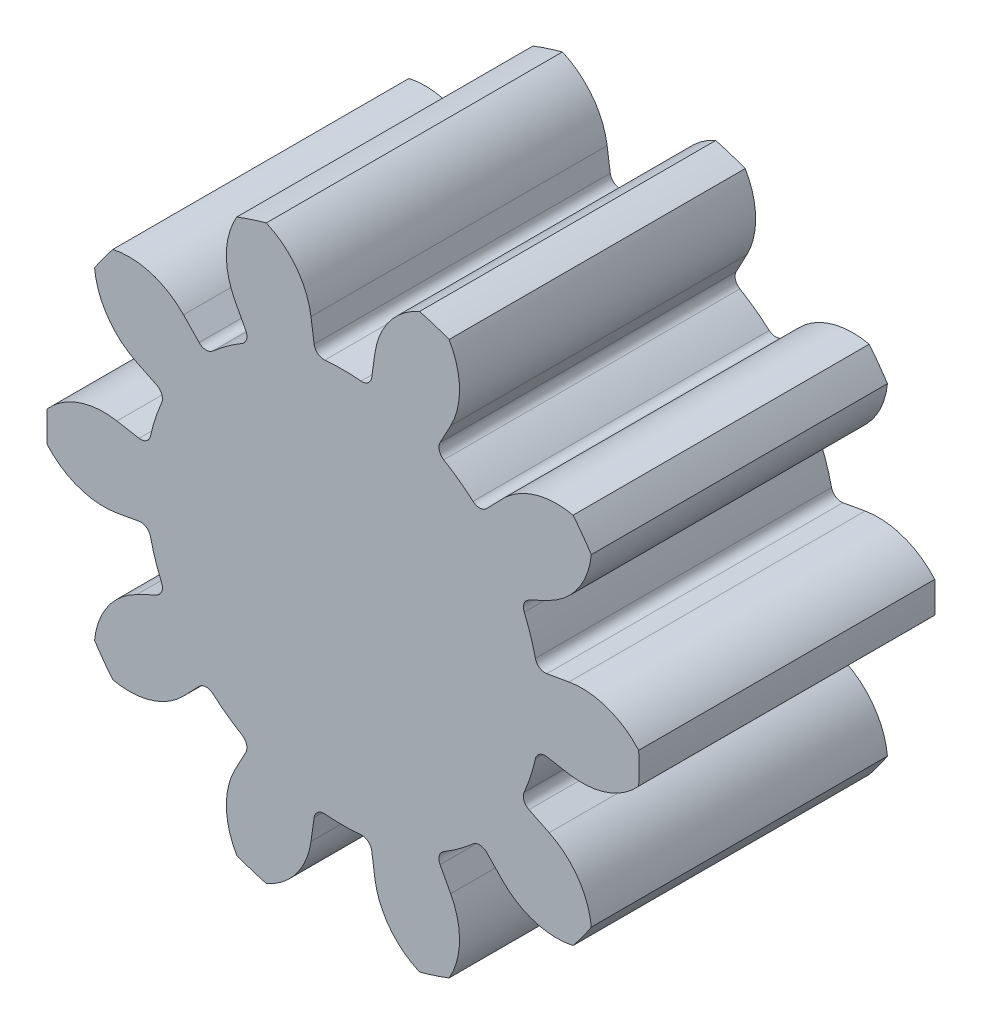
SolidWorks part; units mm, degrees
ref_plane "Front Plane" through (0, 0, 0) normal (0, 0, 1) x (1, 0, 0)
ref_plane "Top Plane" through (0, 0, 0) normal (0, 1, 0) x (1, 0, 0)
ref_plane "Right Plane" through (0, 0, 0) normal (1, 0, 0) x (0, 0, -1)
sketch "Sketch1" plane through (0, 0, 0) normal (0, 0, 1) x (1, 0, 0)
  line L0 (0, 0) -> (9.7603, 0) construction
  line L1 (0, 0) -> (9.1385, 2.9693) construction
  line L2 (0, 0) -> (9.3575, 1.65) construction
  line L3 (0, 0) -> (7.8775, 0.4128) construction
  line L4 (4.5794, 0.8075) -> (3.9376, 0.6943)
  line L5 (0, 0) -> (3.8027, 1.2356)
  line L6 (4.5794, -0.8075) -> (3.9376, -0.6943)
  line L7 (0, 0) -> (3.8027, -1.2356)
  circle A0 centre (0, 0) radius 6 construction
  circle A1 centre (0, 0) radius 4.65 construction
  circle A2 centre (0, 0) radius 4 construction
  arc A3 (4.5794, 0.8075) -> (5.9918, 0.314) centre (4.8451, -0.6999) cw
  arc A4 (3.8027, 1.2356) -> (3.9376, 0.6943) centre (0, 0) cw
  arc A5 (5.9918, 0.314) -> (5.9918, -0.314) centre (0, 0) cw
  arc A6 (4.5794, -0.8075) -> (5.9918, -0.314) centre (4.8451, 0.6999) ccw
  arc A7 (3.8027, -1.2356) -> (3.9376, -0.6943) centre (0, 0) ccw
  dimension "D1" = 12
  dimension "D2" = 8
  dimension "D3" = 9.3
  dimension "D4" = 18
  dimension "D5" = 10
  dimension "D6" = 3
extrude "Boss-Extrude1" add sketch "Sketch1" along normal blind 6 contours L7 A7 L6 A6 A5 A3 L4 A4 L5
fillet "Fillet3" radius 0.2 1 edges at (3.9376, 0.6943, 3)
fillet "Fillet4" radius 0.2 1 edges at (3.9376, -0.6943, 3)
pattern_circular "CirPattern1" count 10 over 360 about axis through (0, 0, 0) along (0, 0, 1) of "Boss-Extrude1", "Fillet3", "Fillet4"
